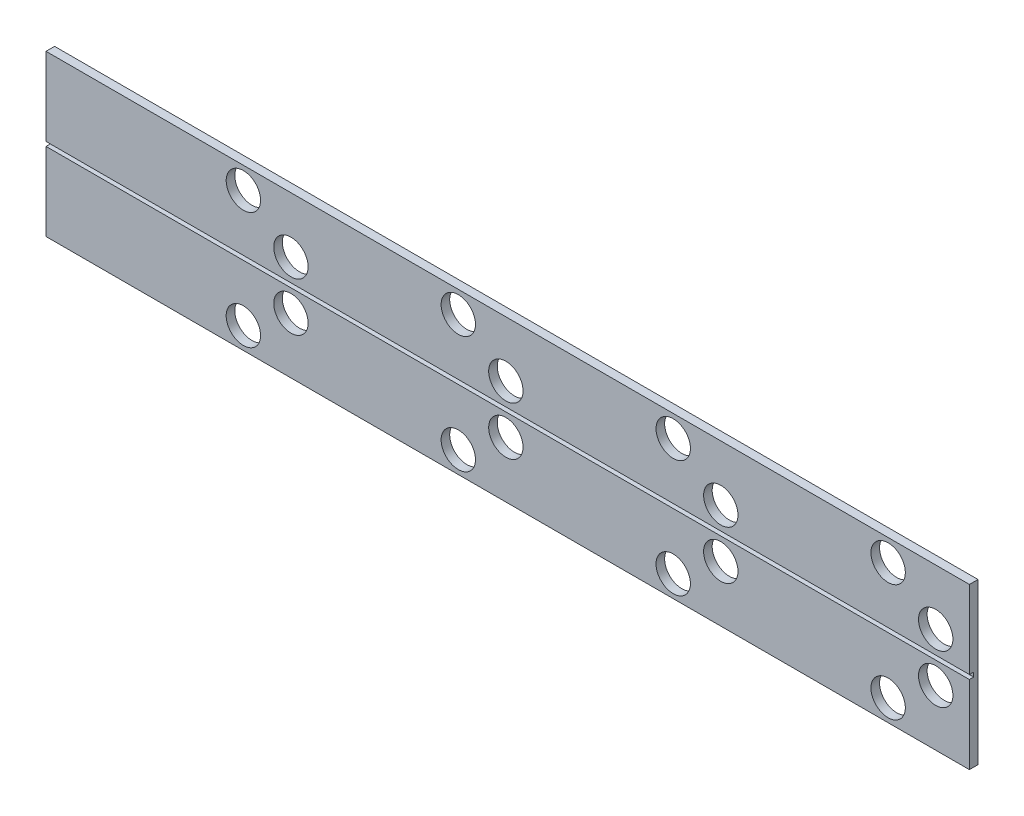
SolidWorks part; units mm, degrees
ref_plane "Ebene vorne" through (0, 0, 0) normal (0, 0, 1) x (1, 0, 0)
ref_plane "Ebene oben" through (0, 0, 0) normal (0, 1, 0) x (1, 0, 0)
ref_plane "Ebene rechts" through (0, 0, 0) normal (1, 0, 0) x (0, 0, -1)
sketch "Skizze1" plane through (0, 0, 0) normal (0, 0, 1) x (1, 0, 0)
  line L1 (-10.7411, 1.866) -> (10.7411, 1.866)
  line L2 (-10.7411, 1.866) -> (-10.7411, -1.866)
  line L3 (-10.7411, -1.866) -> (10.7411, -1.866)
  line L4 (10.7411, 1.866) -> (10.7411, -1.866)
  line L5 (-10.7411, 1.866) -> (10.7411, -1.866) construction
  line L6 (-10.7411, -1.866) -> (10.7411, 1.866) construction
  point P0 (0, 0)
extrude "Aufsatz-Linear austragen1" add sketch "Skizze1" along normal blind 0.2
sketch "Skizze2" plane through (0, 0, 0.2) normal (0, 0, 1) x (1, 0, 0)
  line L0 (-10.7411, 1.866) -> (-10.7411, -1.866) construction
  line L1 (10.7411, -0.05) -> (-10.7411, -0.05)
  line L2 (10.7411, -0.05) -> (10.7411, 0.05)
  line L3 (10.7411, 0.05) -> (-10.7411, 0.05)
  line L4 (-10.7411, -0.05) -> (-10.7411, 0.05)
  line L5 (10.7411, -0.05) -> (-10.7411, 0.05) construction
  line L6 (10.7411, 0.05) -> (-10.7411, -0.05) construction
  point P0 (0, 0)
  dimension "D1" = 0.1
extrude "Schnitt-Linear austragen1" cut sketch "Skizze2" against normal blind 0.1
sketch "Skizze3" plane through (0, 0, 0.2) normal (0, 0, 1) x (1, 0, 0)
  circle A0 centre (9.9572, -0.5629) radius 0.4
  circle A1 centre (8.8506, -1.3652) radius 0.4
  circle A2 centre (9.9572, 0.5713) radius 0.4
  circle A3 centre (8.8506, 1.3597) radius 0.4
extrude "Schnitt-Linear austragen2" cut sketch "Skizze3" against normal through all
pattern_linear "Lineares Muster1" count 4 spacing 5 along (-1, 0, 0) of "Schnitt-Linear austragen2"
other "Fläche löschen1" [suppressed]
other "Fläche löschen2" [suppressed]
